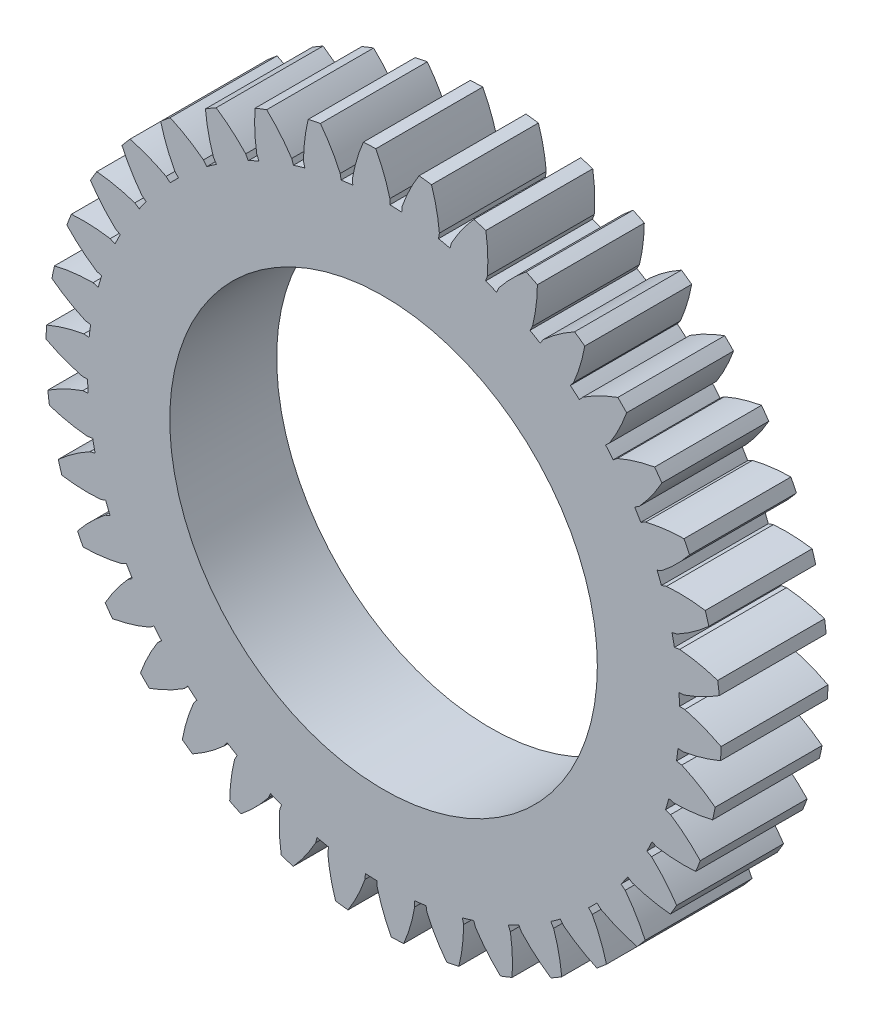
SolidWorks part; units mm, degrees
ref_plane "Front Plane" through (0, 0, 0) normal (0, 0, 1) x (1, 0, 0)
ref_plane "Top Plane" through (0, 0, 0) normal (0, 1, 0) x (1, 0, 0)
ref_plane "Right Plane" through (0, 0, 0) normal (1, 0, 0) x (0, 0, -1)
sketch "Sketch1" plane through (0, 0, 0) normal (0, 0, 1) x (1, 0, 0)
  line L0 (0, 0) -> (0, 84.1652) construction
  line L1 (-57.9961, 38.1) -> (60.5542, 38.1) construction
  line L2 (-56.6662, 17.4752) -> (60.5563, 60.1407) construction
  line L3 (0, 0) -> (-12.2451, 33.6431) construction
  line L4 (-12.2451, 33.6431) -> (0, 38.1)
  line L5 (-17.996, 30.9507) -> (0, 0) construction
  line L6 (-17.996, 30.9507) -> (-1.2414, 40.6926) construction
  line L7 (-2.3014, 35.7282) -> (0, 0) construction
  line L8 (-2.3014, 35.7282) -> (4.0355, 36.1364) construction
  line L9 (0, 0) -> (-3.5147, 84.9787) construction
  line L10 (0.7498, 35.1593) -> (0.7498, 35.7944)
  line L11 (-3.6507, 34.9773) -> (-3.7031, 35.6103)
  circle A0 centre (0, 0) radius 38.1 construction
  circle A1 centre (0, 0) radius 35.8023 construction
  arc A2 (-12.2451, 33.6431) -> (-17.996, 30.9507) centre (0, 0) ccw
  arc A3 (-12.2451, 33.6431) -> (-2.3014, 35.7282) centre (0, 0) cw
  arc A4 (-0.9148, 40.0962) -> (-2.3994, 40.0348) centre (0, 0) ccw
  arc A5 (-3.6507, 34.9773) -> (0.7498, 35.1593) centre (0, 0) cw
  arc A6 (2.9529, 35.1372) -> (0.7498, 35.1593) centre (1.4996, 0) ccw
  circle A7 centre (0, 0) radius 35.1673
  spline S0 degree 3 poles (-0.9148, 40.0962) (-0.1952, 38.7282) (0.3597, 37.2943) (0.7498, 35.7944) knots 0.127669 0.127669 0.127669 0.127669 1 1 1 1
  spline S1 degree 3 poles (-2.3994, 40.0348) (-3.0036, 38.612) (-3.4382, 37.1372) (-3.7031, 35.6103) knots 0.127669 0.127669 0.127669 0.127669 1 1 1 1
  point P8 (0, 38.1)
  dimension "D1" = 76.2
  dimension "D10" = 80.2132
  dimension "D2" = 20
  dimension "D3" = 13.031
  dimension "D4" = 6.35
  dimension "D5" = 19.381
  dimension "D6" = 10.16
  dimension "D7" = 6.35
  dimension "D8" = 0.7498
  dimension "D9" = 2.368
  dimension "D11" = 0.635
sketch "Sketch2" plane through (0, 0, 0) normal (0, 0, 1) x (1, 0, 0)
  line L0 (-12.2451, 33.6431) -> (0, 38.1) construction
  line L1 (-12.2451, 33.6431) -> (0, 38.1)
  line L2 (0.7498, 35.1593) -> (0.7498, 35.7944)
  line L3 (-3.7031, 35.6103) -> (-3.6507, 34.9773)
  line L4 (0.7498, 35.1593) -> (0.7498, 35.7944)
  line L5 (-3.7031, 35.6103) -> (-3.6507, 34.9773)
  arc A0 (-2.3014, 35.7282) -> (-12.2451, 33.6431) centre (0, 0) ccw construction
  circle A1 centre (0, 0) radius 35.1673
  circle A2 centre (0, 0) radius 35.1673
  arc A3 (-12.2451, 33.6431) -> (-17.996, 30.9507) centre (0, 0) ccw construction
  arc A4 (-0.9148, 40.0962) -> (-2.3994, 40.0348) centre (0, 0) ccw
  arc A5 (0.7498, 35.1593) -> (-3.6507, 34.9773) centre (0, 0) ccw
  arc A6 (-0.9148, 40.0962) -> (-2.3994, 40.0348) centre (0, 0) ccw
  arc A7 (0.7498, 35.1593) -> (-3.6507, 34.9773) centre (0, 0) ccw
  arc A8 (2.9529, 35.1372) -> (0.7498, 35.1593) centre (1.4996, 0) ccw construction
  arc A9 (-2.3014, 35.7282) -> (-12.2451, 33.6431) centre (0, 0) ccw
  arc A10 (-12.2451, 33.6431) -> (-17.996, 30.9507) centre (0, 0) ccw
  arc A11 (2.9529, 35.1372) -> (0.7498, 35.1593) centre (1.4996, 0) ccw
  parabola Q2 (0.7498, 35.7944) -> (-0.9148, 40.0962) focus (-9.3158, 34.4946) apex (-0.0414, 38.2043)
  parabola Q3 (-2.3994, 40.0348) -> (-3.7031, 35.6103) focus (6.4355, 35.1461) apex (-3.1136, 38.0773)
  parabola Q4 (0.7498, 35.7944) -> (-0.9148, 40.0962) focus (-9.3158, 34.4946) apex (-0.0414, 38.2043)
  parabola Q5 (-2.3994, 40.0348) -> (-3.7031, 35.6103) focus (6.4355, 35.1461) apex (-3.1136, 38.0773)
  point P0 (-2.3014, 35.7282)
  dimension "D1" = 0
  dimension "D2" = 0
extrude "Boss-Extrude1" add sketch "Sketch2" along normal blind 12.7 contours A2
extrude "Boss-Extrude2" add sketch "Sketch1" along normal up to surface (12.7 mm away) contours A5 L11 S1 A4 S0 L10 up to face at (35.1673, 0, 12.7)
pattern_circular "CirPattern1" count 38 over 360 about axis through (0, 0, 12.7) along (0, 0, 1) of "Boss-Extrude2"
sketch "Sketch3" plane through (0, 0, 12.7) normal (0, 0, 1) x (1, 0, 0)
  circle A0 centre (0, 0) radius 25.4
  dimension "D1" = 50.8
extrude "Cut-Extrude1" cut sketch "Sketch3" against normal blind 12.7
equation "\"D5@Sketch1\"=\"D3@Sketch1\"+\"D4@Sketch1\""
equation "\"D7@Sketch1\"=\"D5@Sketch1\"-\"D3@Sketch1\""
equation "\"D9@Sketch1\"=360/38/4"
equation "\"D10@Sketch1\"=\"D1@Sketch1\"+(2*.079)"
